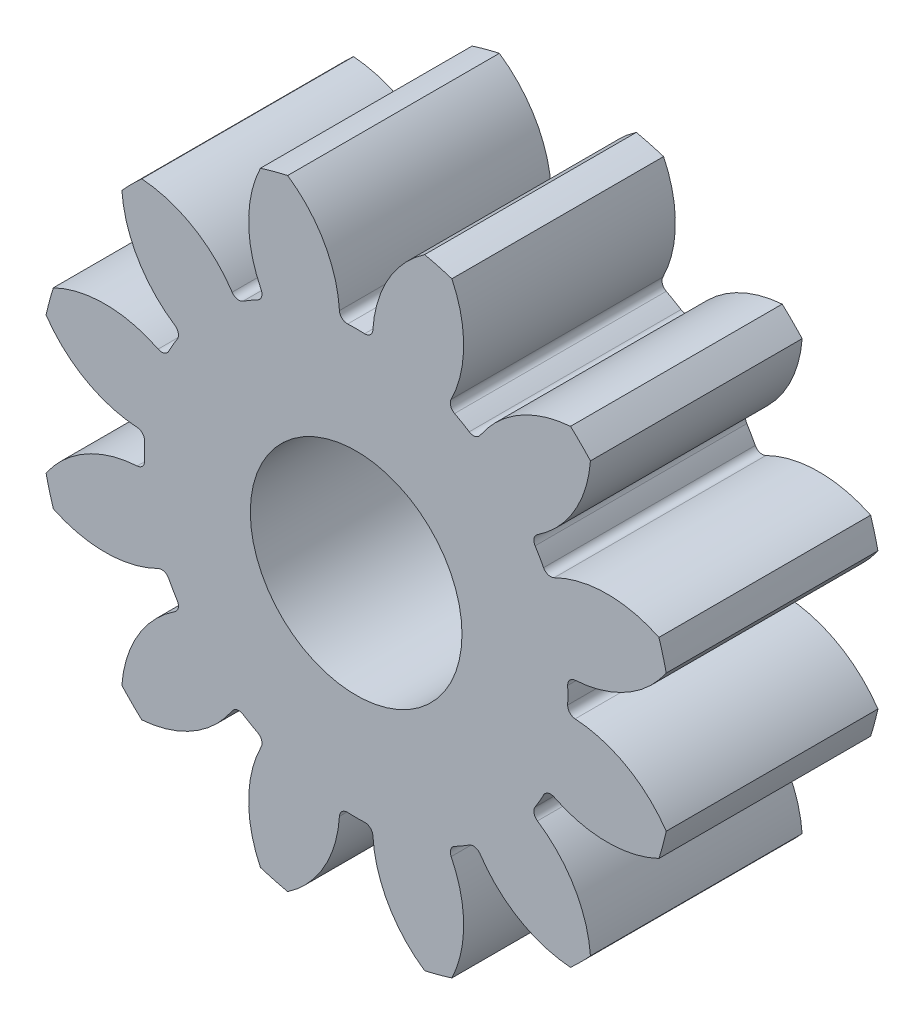
SolidWorks part; units mm, degrees
ref_plane "Front" through (0, 0, 0) normal (0, 0, 1) x (1, 0, 0)
ref_plane "Top" through (0, 0, 0) normal (0, 1, 0) x (1, 0, 0)
ref_plane "Right" through (0, 0, 0) normal (1, 0, 0) x (0, 0, -1)
sketch "Sketch1" plane through (0, 0, 0) normal (0, 0, 1) x (1, 0, 0)
  circle A0 centre (0, 0) radius 2
  circle A1 centre (0, 0) radius 6
extrude "Boss-Extrude1" add sketch "Sketch1" along normal blind 4
sketch "Sketch4" plane through (0, 0, 0) normal (0, 0, 1) x (1, 0, 0)
  arc A0 (-0.1602, 3.9968) -> (-0.3159, 4.1375) centre (-0.1662, 4.1467) cw
  arc A1 (0.1602, 3.9968) -> (-0.1602, 3.9968) centre (0, 0) ccw
  arc A2 (-0.3159, 4.1375) -> (-2.0102, 6.1814) centre (-2.5617, 4) ccw
  arc A3 (2.0102, 6.1814) -> (0.3159, 4.1375) centre (2.5617, 4) ccw
  arc A4 (0.1602, 3.9968) -> (0.3159, 4.1375) centre (0.1662, 4.1467) ccw
  arc A5 (2.0102, 6.1814) -> (-2.0102, 6.1814) centre (0, 0) ccw
  dimension "D1" = 0.15
  dimension "D2" = 0.15
extrude "Cut-Extrude2" cut sketch "Sketch4" along normal through all
pattern_circular "CirPattern2" count 12 over 360 about axis through (0, 0, 0) along (0, 0, 1) of "Cut-Extrude2"
sketch "Sketch10" plane through (0, 0, 0) normal (0, 0, 1) x (1, 0, 0)
  line L0 (0, 4) -> (-5.1235, 4) construction
  line L1 (0, 4) -> (5.1235, 4) construction
  circle A0 centre (0, 0) radius 6.5
  circle A1 centre (0, 0) radius 4
  circle A2 centre (-2.5617, 4) radius 2.25
  circle A3 centre (2.5617, 4) radius 2.25
